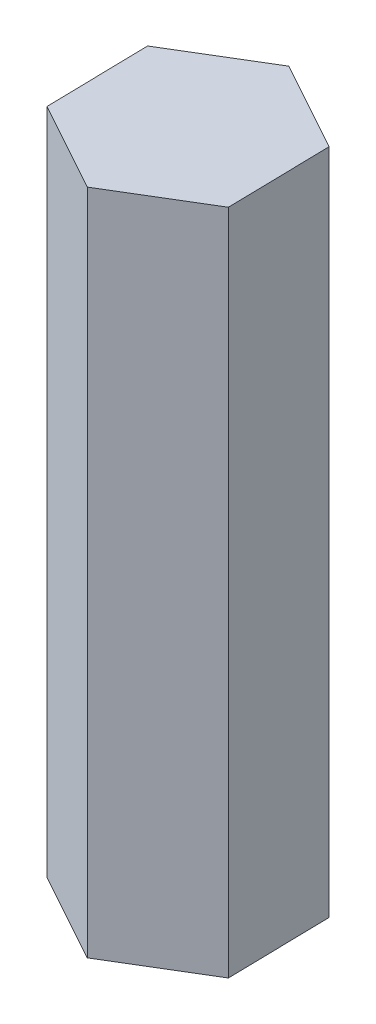
SolidWorks part; units mm, degrees
ref_plane "前视基准面" through (0, 0, 0) normal (0, 0, 1) x (1, 0, 0)
ref_plane "上视基准面" through (0, 0, 0) normal (0, 1, 0) x (1, 0, 0)
ref_plane "右视基准面" through (0, 0, 0) normal (1, 0, 0) x (0, 0, -1)
sketch "草图1" plane through (0, 0, 0) normal (0, 1, 0) x (1, 0, 0)
  line L1 (4.0451, -2.2294) -> (3.9533, 2.3885)
  line L2 (3.9533, 2.3885) -> (-0.0918, 4.6179)
  line L3 (-0.0918, 4.6179) -> (-4.0451, 2.2294)
  line L4 (-4.0451, 2.2294) -> (-3.9533, -2.3885)
  line L5 (-3.9533, -2.3885) -> (0.0918, -4.6179)
  line L6 (0.0918, -4.6179) -> (4.0451, -2.2294)
  circle A0 centre (0, 0) radius 4 construction
extrude "凸台-拉伸1" add sketch "草图1" along normal blind 30
sketch "草图2" plane through (0, 30, 0) normal (0, 1, 0) x (1, 0, 0)
  circle A0 centre (0, 0) radius 2
